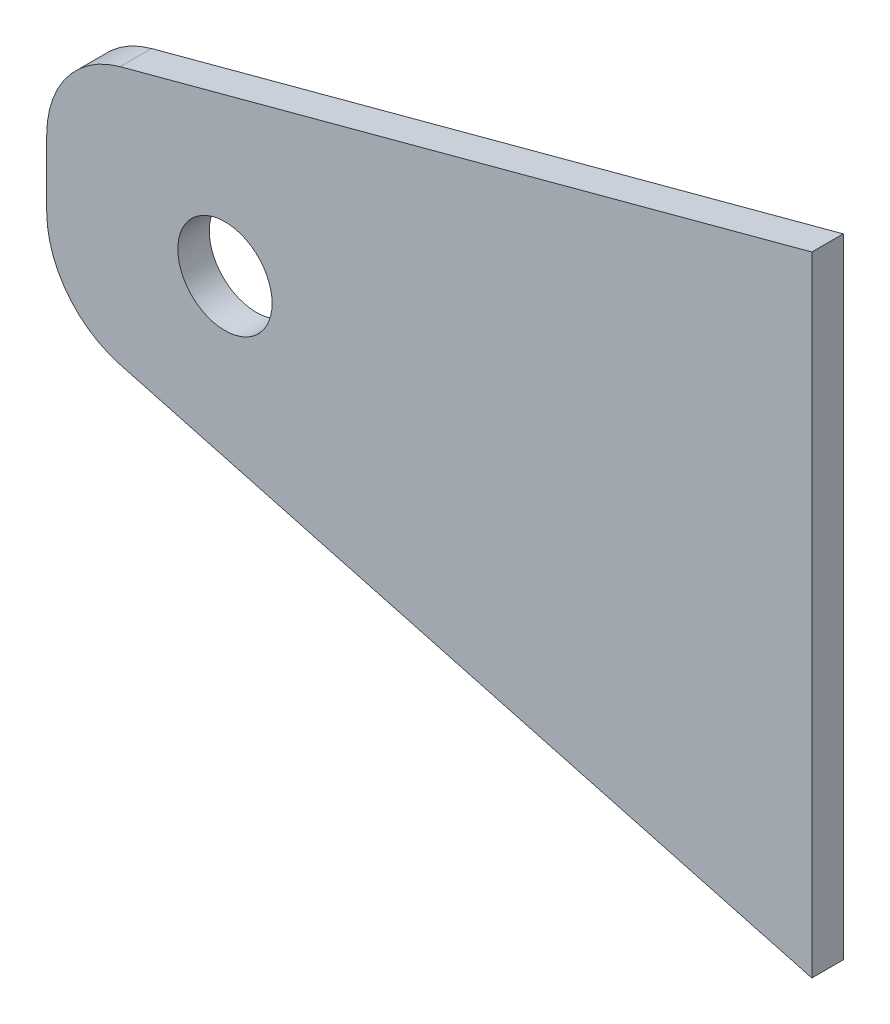
SolidWorks part; units mm, degrees
ref_plane "Alzado" through (0, 0, 0) normal (0, 0, 1) x (1, 0, 0)
ref_plane "Planta" through (0, 0, 0) normal (0, 1, 0) x (1, 0, 0)
ref_plane "Vista lateral" through (0, 0, 0) normal (1, 0, 0) x (0, 0, -1)
sketch "Croquis1" plane through (0, 0, 0) normal (0, 0, 1) x (1, 0, 0)
  line L0 (0, 0) -> (0, 63.5)
  line L1 (0, 63.5) -> (-77.2741, 42.7945)
  line L2 (0, 0) -> (-77.2741, 20.7055)
  line L3 (-77.2741, 42.7945) -> (-77.2741, 20.7055)
  dimension "D1" = 63.5
  dimension "D2" = 75
  dimension "D3" = 75
  dimension "D4" = 80
extrude "Saliente-Extruir1" add sketch "Croquis1" along normal blind 3.175
sketch "Croquis2" plane through (0, 0, 3.175) normal (0, 0, 1) x (1, 0, 0)
  line L0 (-77.2741, 31.75) -> (-59.2741, 31.75) construction
  line L1 (-77.2741, 42.7945) -> (-77.2741, 20.7055) construction
  circle A0 centre (-59.2741, 31.75) radius 4.7625
  dimension "D2" = 9.525
  dimension "D1" = 18
extrude "Cortar-Extruir1" cut sketch "Croquis2" against normal blind 3.175
fillet "Redondeo1" radius 10 2 edges at (-77.2741, 20.7055, 1.5875) (-77.2741, 42.7945, 1.5875)
